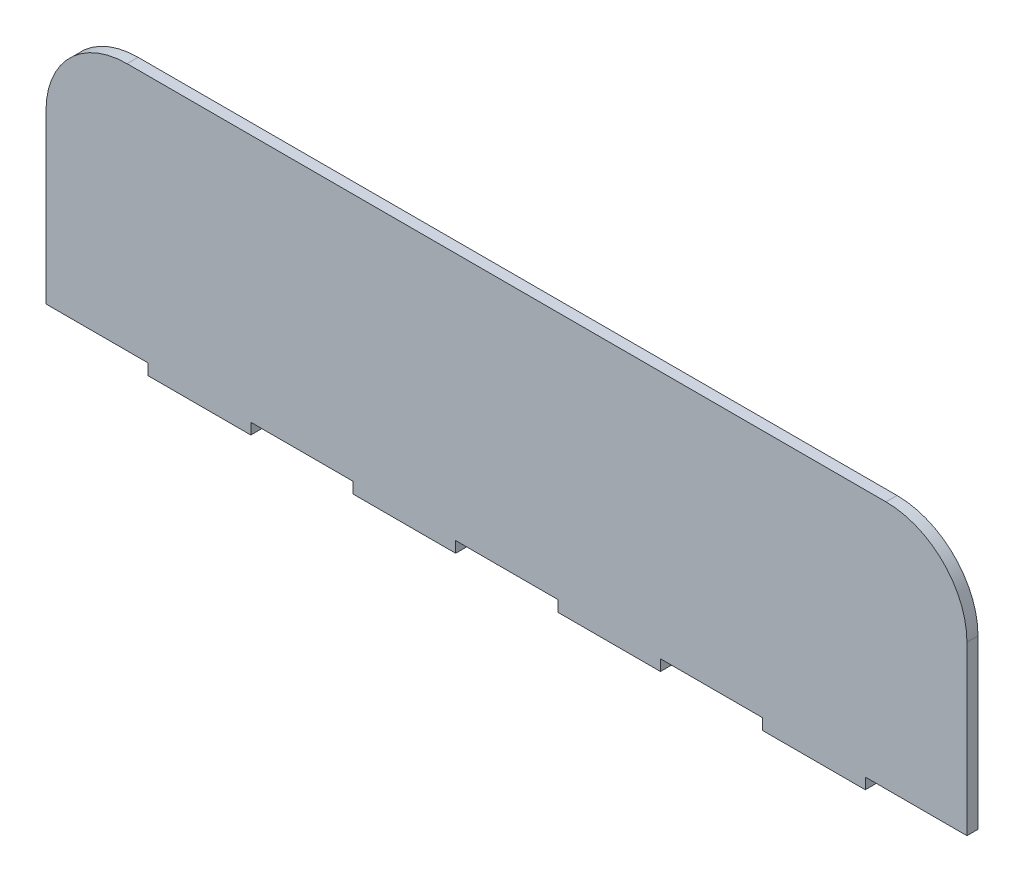
SolidWorks part; units mm, degrees
material "Pine"
ref_plane "Front Plane" through (0, 0, 0) normal (0, 0, 1) x (1, 0, 0)
ref_plane "Top Plane" through (0, 0, 0) normal (0, 1, 0) x (1, 0, 0)
ref_plane "Right Plane" through (0, 0, 0) normal (1, 0, 0) x (0, 0, -1)
sketch "Sketch1" plane through (0, 0, 0) normal (0, 0, 1) x (1, 0, 0)
  line L1 (0, 0) -> (500, 0)
  line L2 (0, 0) -> (0, 501)
  line L3 (0, 501) -> (500, 501)
  line L4 (500, 0) -> (500, 501)
  dimension "D1" = 500
  dimension "D2" = 501
extrude "Boss-Extrude1" add sketch "Sketch1" along normal blind 6
fillet "Fillet1" radius 44 4 edges at (0, 0, 3) (0, 501, 3) (500, 0, 3) (500, 501, 3)
sketch "Sketch2" plane through (0, 0, 0) normal (0, 0, -1) x (-1, 0, 0)
  line L0 (-456, 501) -> (-44, 501) construction
  line L1 (0, 360) -> (-55.5, 360)
  line L2 (0, 360) -> (0, 366)
  line L3 (0, 366) -> (-55.5, 366)
  line L4 (-55.5, 360) -> (-55.5, 366)
  line L5 (0, 457) -> (0, 44) construction
  dimension "D1" = 135
  dimension "D2" = 6
  dimension "D3" = 0
  dimension "D4" = 55.5
extrude "Cut-Extrude1" cut sketch "Sketch2" against normal blind 10
pattern_linear "LPattern1" count 5 spacing 111.2 along (1, 0, 0) of "Cut-Extrude1"
sketch "Sketch3" plane through (0, 0, 0) normal (0, 0, -1) x (-1, 0, 0)
  line L1 (-500, 360) -> (0, 360)
  line L2 (-500, 360) -> (-500, 0)
  line L3 (-500, 0) -> (0, 0)
  line L4 (0, 360) -> (0, 0)
extrude "Cut-Extrude2" cut sketch "Sketch3" against normal blind 10
